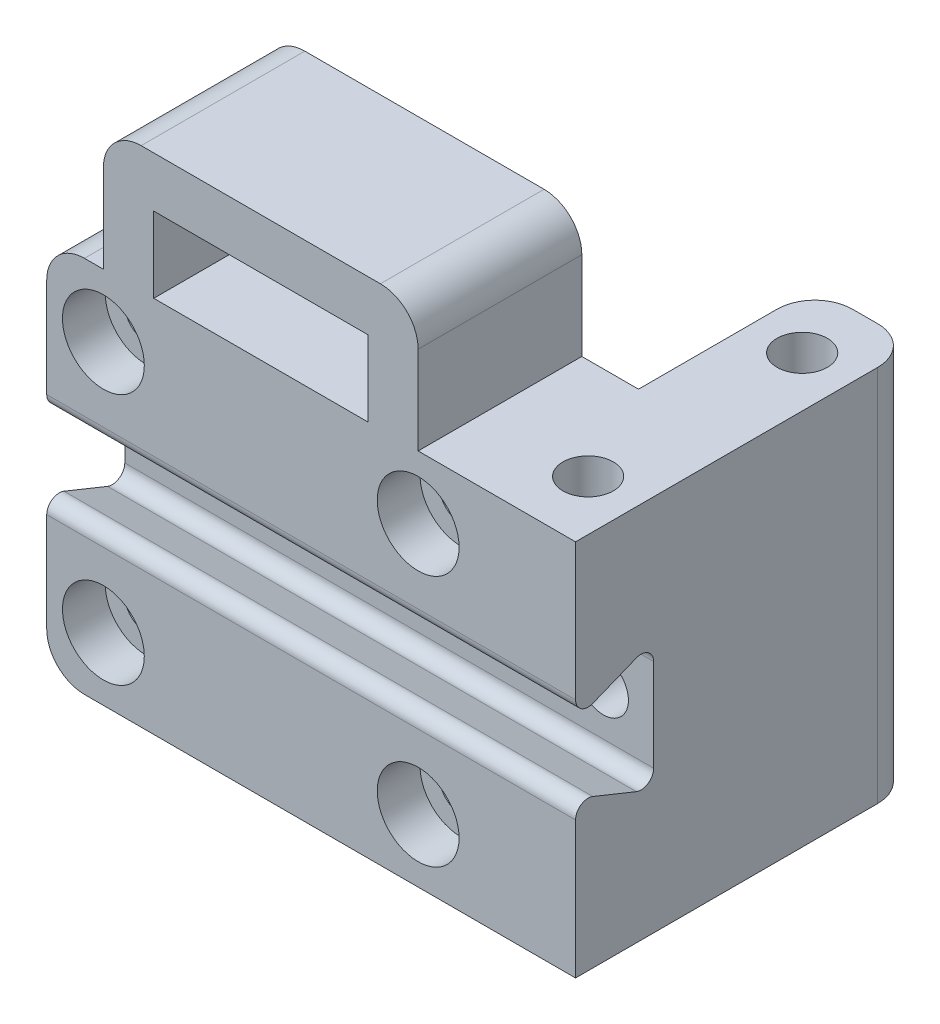
SolidWorks part; units mm, degrees
material "PUR"
ref_plane "Ebene vorne" through (0, 0, 0) normal (0, 0, 1) x (1, 0, 0)
ref_plane "Ebene oben" through (0, 0, 0) normal (0, 1, 0) x (1, 0, 0)
ref_plane "Ebene rechts" through (0, 0, 0) normal (1, 0, 0) x (0, 0, -1)
sketch "Skizze1" plane through (0, 0, 0) normal (0, 0, 1) x (1, 0, 0)
  line L1 (17, -15) -> (-17, -15)
  line L2 (17, -15) -> (17, 15)
  line L3 (17, 15) -> (-17, 15)
  line L4 (-17, -15) -> (-17, 15)
  line L5 (17, -15) -> (-17, 15) construction
  line L6 (17, 15) -> (-17, -15) construction
  point P0 (0, 0)
  dimension "D1" = 30
  dimension "D2" = 34
extrude "Aufsatz-Linear austragen1" add sketch "Skizze1" along normal blind 13
hole_wizard "Stirnsenkung für M3 Zylinderschraube mit Innensechskant1" positions "Skizze2" profile "Skizze3" counterbore size "M3" standard "ISO" end condition through all
sketch "Skizze2" plane through (0, 0, 13) normal (0, 0, 1) x (1, 0, 0)
  line L0 (12.5, 10) -> (-12.5, 10) construction
  line L1 (-12.5, 10) -> (-12.5, -10) construction
  line L2 (-12.5, -10) -> (12.5, -10) construction
  line L3 (12.5, -10) -> (12.5, 10) construction
  point P0 (-12.5, 10)
  point P2 (-12.5, -10)
  point P4 (12.5, -10)
  point P6 (12.5, 10)
  point P16 (0, 10)
  point P18 (-12.5, 0)
  dimension "D1" = 20
  dimension "D2" = 25
sketch "Skizze3" plane through (-12.5, 10, 13) normal (1, 0, 0) x (0, -1, 0)
  line L0 (0, 0) -> (0, 13)
  line L1 (0, 13) -> (1.7, 13)
  line L3 (1.7, 13) -> (1.7, 3.4)
  line L4 (1.7, 3.4) -> (3.25, 3.4)
  line L5 (3.25, 3.4) -> (3.25, 0)
  line L7 (3.25, 0) -> (0, 0)
  line L11 (0, -6.35) -> (0, 107.95) construction
  dimension "Bohrerdurchmesser" = 3.4
  dimension "Bohrungstiefe" = 13
  dimension "Senkdurchmesser2" = 6.5
  dimension "Senktiefe2" = 3.4
sketch "Skizze4" plane through (0, 15, 0) normal (0, 1, 0) x (1, 0, 0)
  line L0 (17, 0) -> (-17, 0) construction
  line L1 (17, -13) -> (25, -13)
  line L2 (17, -13) -> (17, 14)
  line L3 (17, 14) -> (25, 14)
  line L4 (25, -13) -> (25, 14)
  dimension "D1" = 14
  dimension "D2" = 8
extrude "Aufsatz-Linear austragen2" add sketch "Skizze4" against normal through all
hole_wizard "Ø4.0 (4) Durchmesser Bohrung1" positions "Skizze5" profile "Skizze6" hole size "Ø4.0" standard "ISO"
sketch "Skizze5" plane through (0, 15, 0) normal (0, 1, 0) x (1, 0, 0)
  line L0 (21, 14) -> (21, -13) construction
  line L1 (25, 14) -> (17, 14) construction
  line L2 (25, -13) -> (-17, -13) construction
  point P9 (21, 9)
  point P11 (21, -8)
  dimension "D1" = 17
  dimension "D2" = 5
sketch "Skizze6" plane through (21, 15, 8) normal (1, 0, 0) x (0, 0, 1)
  line L0 (0, 0) -> (0, 6.2017)
  line L1 (0, 6.2017) -> (2, 5)
  line L2 (2, 5) -> (2, 0)
  line L5 (2, 0) -> (0, 0)
  line L10 (0, 6.2017) -> (-2, 5) construction
  line L11 (0, -6.35) -> (0, 107.95) construction
  dimension "Bohrerdurchmesser" = 4
  dimension "Bohrungstiefe" = 5
  dimension "Spitzenwinkel" = 118
mirror "Spiegeln1" about plane through (0, 0, 0) normal (0, 1, 0) of "Ø4.0 (4) Durchmesser Bohrung1"
sketch "Skizze7" plane through (-17, 0, 0) normal (-1, 0, 0) x (0, 0, 1)
  line L0 (13, 2.65) -> (6.8, 5.15)
  line L1 (13, 15) -> (13, -15) construction
  line L2 (6.8, 5.15) -> (6.8, -5.15)
  line L3 (6.8, -5.15) -> (13, -2.65)
  line L4 (13, -2.65) -> (13, 2.65)
  point P5 (13, 0)
  dimension "D1" = 6.2
  dimension "D2" = 10.3
  dimension "D3" = 5.3
extrude "Schnitt-Linear austragen1" cut sketch "Skizze7" against normal through all
sketch "Skizze10" plane through (0, 0, 0) normal (0, 0, -1) x (-1, 0, 0)
  line L0 (-17, 15) -> (17, 15) construction
  line L1 (-12.5, 15) -> (-8.5, 15)
  line L2 (-12.5, 15) -> (-12.5, 25)
  line L3 (-12.5, 25) -> (12.5, 25)
  line L4 (12.5, 15) -> (12.5, 25)
  line L5 (-12.5, 10) -> (-12.5, 15) construction
  line L6 (12.5, 10) -> (12.5, 15) construction
  line L7 (-8.5, 15) -> (-8.5, 21)
  line L8 (-8.5, 21) -> (8.5, 21)
  line L9 (8.5, 15) -> (8.5, 21)
  line L10 (8.5, 15) -> (12.5, 15)
  dimension "D1" = 10
  dimension "D2" = 4
extrude "Aufsatz-Linear austragen3" add sketch "Skizze10" against normal up to surface (13 mm away) up to face at (4, 8.825, 13)
ref_plane "Ebene1" through (17, -15, -14) normal (0, 1, 0) x (1, 0, 0)
fillet "Verrundung2" radius 3 4 edges at (-17, 15, 6.5) (-17, -15, 6.5) (-12.5, 25, 6.5) (12.5, 25, 6.5)
fillet "Verrundung1" radius 3 2 edges at (17, 0, -14) (25, 0, -14)
fillet "Verrundung4" radius 1 4 edges at (4, 2.65, 13) (4, -2.65, 13) (4, -5.15, 6.8) (4, 5.15, 6.8)
hole_wizard "Ø4.0 (4) Durchmesser Bohrung2" positions "Skizze8" profile "Skizze9" hole size "Ø4.0" standard "ISO"
sketch "Skizze8" plane through (0, 0, 6.8) normal (0, 0, 1) x (1, 0, 0)
  line L0 (21, 0) -> (0, 0) construction
  line L3 (25, 3.6685) -> (25, -3.6685) construction
  point P0 (21, 0)
  dimension "D1" = 4
sketch "Skizze9" plane through (21, 0, 6.8) normal (1, 0, 0) x (0, -1, 0)
  line L0 (0, 0) -> (0, 6.2017)
  line L1 (0, 6.2017) -> (2, 5)
  line L2 (2, 5) -> (2, 0)
  line L5 (2, 0) -> (0, 0)
  line L10 (0, 6.2017) -> (-2, 5) construction
  line L11 (0, -6.35) -> (0, 107.95) construction
  dimension "Bohrerdurchmesser" = 4
  dimension "Bohrungstiefe" = 5
  dimension "Spitzenwinkel" = 118
